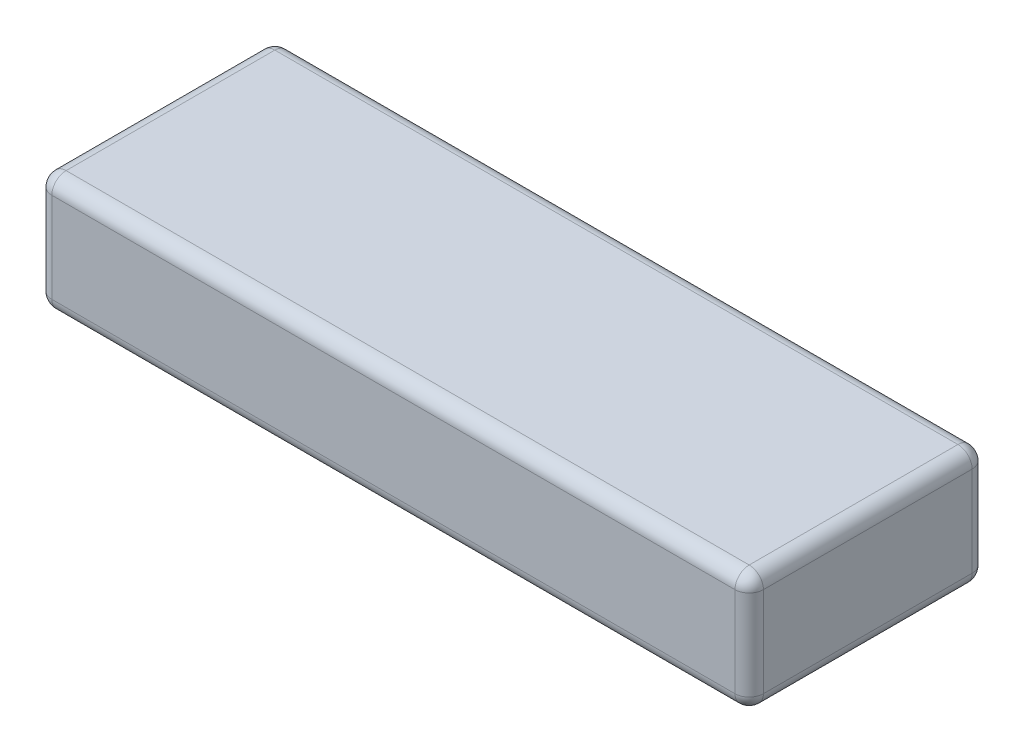
SolidWorks part; units mm, degrees
ref_plane "Front" through (0, 0, 0) normal (0, 0, 1) x (1, 0, 0)
ref_plane "Top" through (0, 0, 0) normal (0, 1, 0) x (1, 0, 0)
ref_plane "Right" through (0, 0, 0) normal (1, 0, 0) x (0, 0, -1)
sketch "Эскиз1" plane through (0, 0, 0) normal (0, 1, 0) x (1, 0, 0)
  line L1 (0, 0) -> (150, 0)
  line L2 (0, 0) -> (0, -50)
  line L3 (0, -50) -> (150, -50)
  line L4 (150, 0) -> (150, -50)
  dimension "D1" = 150
  dimension "D2" = 50
extrude "Бобышка-Вытянуть1" add sketch "Эскиз1" along normal blind 25
fillet "Скругление1" radius 3 12 edges at (75, 25, 50) (75, 0, 0) (0, 12.5, 0) (0, 0, 25) (0, 12.5, 50) (75, 0, 50) (150, 12.5, 0) (150, 0, 25) (150, 12.5, 50) (150, 25, 25) (75, 25, 0) (0, 25, 25)
